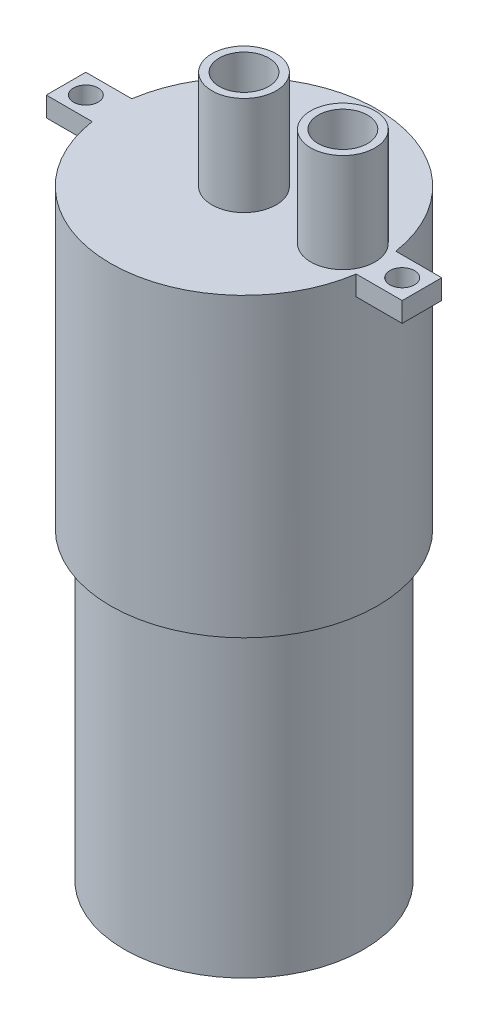
SolidWorks part; units mm, degrees
material "1060 Legierung"
ref_plane "Ebene vorne" through (0, 0, 0) normal (0, 0, 1) x (1, 0, 0)
ref_plane "Ebene oben" through (0, 0, 0) normal (0, 1, 0) x (1, 0, 0)
ref_plane "Ebene rechts" through (0, 0, 0) normal (1, 0, 0) x (0, 0, -1)
sketch "Skizze1" plane through (0, 0, 0) normal (0, 0, 1) x (1, 0, 0)
  line L0 (0, 12.3804) -> (0, 0.7383) construction
  line L1 (0, 0) -> (12.1, 0)
  line L2 (12.1, 0) -> (12.1, 30.8)
  line L3 (12.1, 30.8) -> (13.5, 30.8)
  line L4 (13.5, 30.8) -> (13.5, 60.8)
  line L5 (13.5, 60.8) -> (3.25, 60.8)
  line L6 (3.25, 60.8) -> (3.25, 70.8)
  line L7 (3.25, 70.8) -> (2.5, 70.8)
  line L8 (2.5, 70.8) -> (2.5, 62.8)
  line L9 (2.5, 62.8) -> (0, 62.8)
  line L10 (0, 62.8) -> (0, 0)
  dimension "D1" = 24.2
  dimension "D2" = 27
  dimension "D3" = 6.5
  dimension "D4" = 0.75
  dimension "D5" = 30.8
  dimension "D6" = 30
  dimension "D7" = 10
  dimension "D8" = 8
revolve "Rotation1" add sketch "Skizze1" angle 360 about L0
sketch "Skizze2" plane through (0, 60.8, 0) normal (0, 1, 0) x (1, 0, 0)
  line L0 (10, 0) -> (0, 0) construction
  circle A0 centre (10, 0) radius 3.25
  circle A1 centre (10, 0) radius 2.5
  circle A2 centre (0, 0) radius 3.25 construction
  circle A3 centre (0, 0) radius 2.5 construction
  dimension "D1" = 10
extrude "Aufsatz-Linear austragen1" add sketch "Skizze2" along normal up to surface (10 mm away) up to face at (0, 70.8, 2.5)
sketch "Skizze3" plane through (0, 60.8, 0) normal (0, 1, 0) x (1, 0, 0)
  line L0 (-13.351, 2) -> (-18, 2)
  line L1 (18, -2) -> (13.351, -2)
  line L2 (18, -2) -> (18, 2)
  line L3 (18, 2) -> (13.351, 2)
  line L4 (-18, -2) -> (-18, 2)
  line L5 (18, -2) -> (13.4174, -1.4908) construction
  line L6 (18, 2) -> (13.4174, 1.4908) construction
  line L7 (-13.351, -2) -> (-18, -2)
  line L8 (-13.4174, -1.4908) -> (-18, -2) construction
  line L9 (-13.4174, 1.4908) -> (-18, 2) construction
  line L10 (16, 0) -> (0, 0) construction
  line L11 (0, 0) -> (-16, 0) construction
  circle A0 centre (0, 0) radius 13.5 construction
  arc A1 (-13.351, 2) -> (-13.351, -2) centre (0, 0) ccw
  arc A2 (13.351, -2) -> (13.351, 2) centre (0, 0) ccw
  circle A3 centre (-16, 0) radius 1.25
  circle A4 centre (16, 0) radius 1.25
  point P0 (0, 0)
  dimension "D3" = 32
  dimension "D4" = 2.5
  dimension "D1" = 4
  dimension "D2" = 36
extrude "Aufsatz-Linear austragen2" add sketch "Skizze3" against normal blind 2
